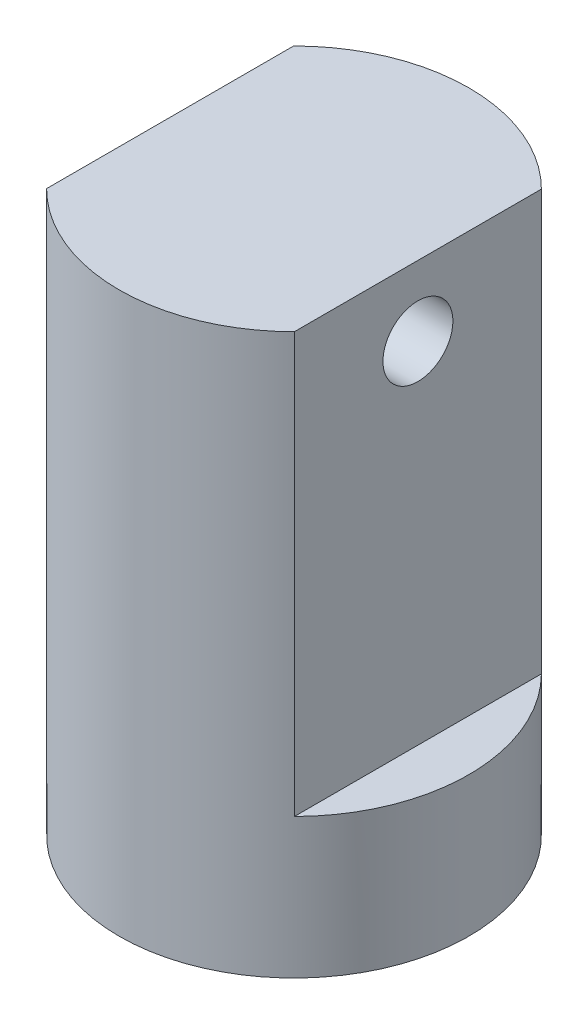
SolidWorks part; units mm, degrees
ref_plane "Front Plane" through (0, 0, 0) normal (0, 0, 1) x (1, 0, 0)
ref_plane "Top Plane" through (0, 0, 0) normal (0, 1, 0) x (1, 0, 0)
ref_plane "Right Plane" through (0, 0, 0) normal (1, 0, 0) x (0, 0, -1)
sketch "Sketch1" plane through (0, 0, 0) normal (0, 1, 0) x (1, 0, 0)
  circle A0 centre (0, 0) radius 25
extrude "Boss-Extrude1" add sketch "Sketch1" along normal blind 80
sketch "Sketch2" plane through (0, 80, 0) normal (0, 1, 0) x (1, 0, 0)
  line L1 (-17.7082, 17.6471) -> (17.7082, 17.6471)
  line L2 (-17.7082, 17.6471) -> (-17.7082, -17.6471)
  line L3 (-17.7082, -17.6471) -> (17.7082, -17.6471)
  line L4 (17.7082, 17.6471) -> (17.7082, -17.6471)
  line L5 (-17.7082, 17.6471) -> (17.7082, -17.6471) construction
  line L6 (-17.7082, -17.6471) -> (17.7082, 17.6471) construction
  circle A0 centre (0, 0) radius 25 construction
  circle A1 centre (0, 0) radius 25
  point P0 (0, 0)
  circle M1 centre (0, 0) radius 25
extrude "Cut-Extrude1" cut sketch "Sketch2" against normal blind 60 contours L2 M1 | L4 M1
sketch "Sketch3" plane through (17.7082, 0, 0) normal (1, 0, 0) x (0, 0, -1)
  circle A0 centre (0, 70) radius 5
extrude "Cut-Extrude2" cut sketch "Sketch3" against normal blind 60
sketch "Sketch4" plane through (0, 0, 0) normal (0, -1, 0) x (1, 0, 0)
  circle A0 centre (0, 0) radius 5
extrude "Cut-Extrude3" cut sketch "Sketch4" against normal blind 30
